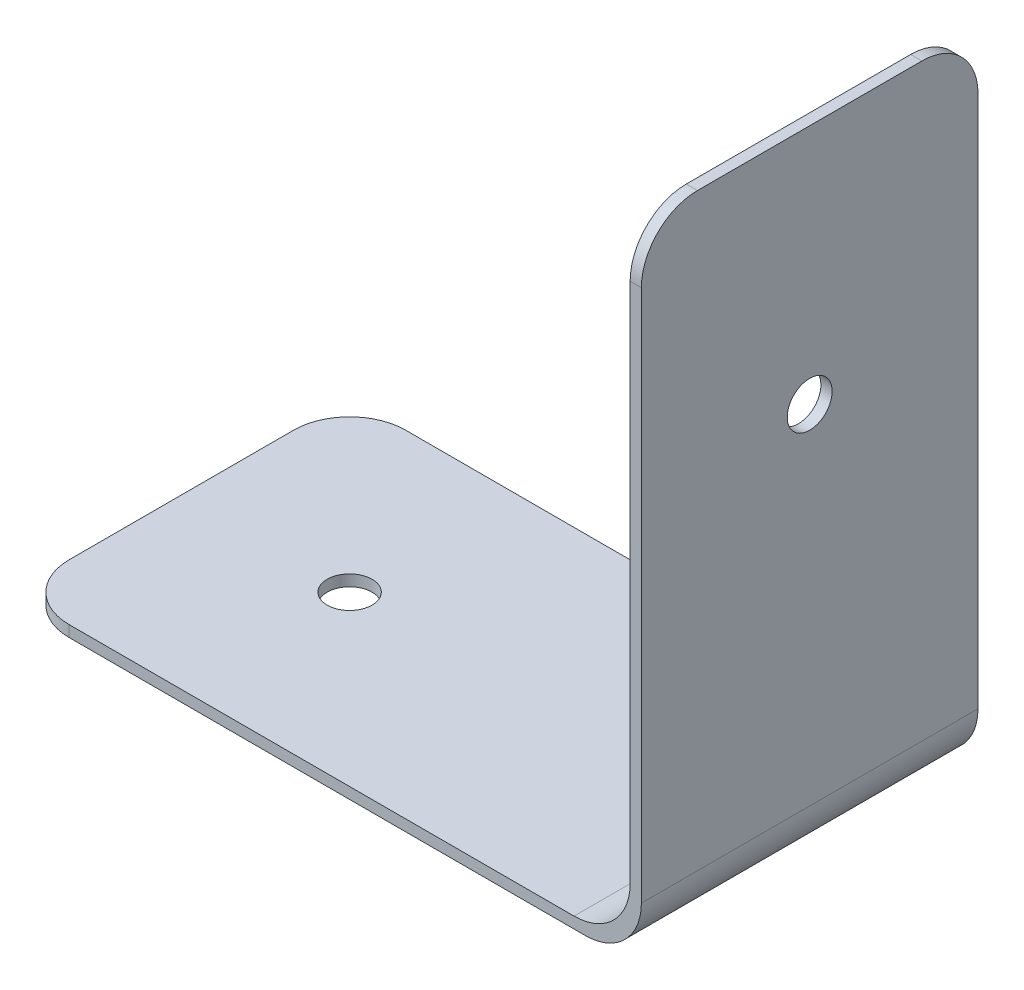
SolidWorks part; units mm, degrees
ref_plane "Front Plane" through (0, 0, 0) normal (0, 0, 1) x (1, 0, 0)
ref_plane "Top Plane" through (0, 0, 0) normal (0, 1, 0) x (1, 0, 0)
ref_plane "Right Plane" through (0, 0, 0) normal (1, 0, 0) x (0, 0, -1)
sketch "Sketch1" plane through (0, 0, 0) normal (0, 0, 1) x (1, 0, 0)
  line L0 (0, 0) -> (102, 0)
  line L1 (112, 10) -> (112, 115)
  line L2 (112, 115) -> (110, 115)
  line L3 (110, 115) -> (110, 12)
  line L4 (0, 0) -> (0, 2)
  line L5 (0, 2) -> (100, 2)
  arc A0 (102, 0) -> (112, 10) centre (102, 10) ccw
  arc A1 (100, 2) -> (110, 12) centre (100, 12) ccw
  dimension "D1" = 10
  dimension "D2" = 2
  dimension "D3" = 2
  dimension "D4" = 100
  dimension "D5" = 105
extrude "Boss-Extrude1" add sketch "Sketch1" along normal blind 60
sketch "Sketch3" plane through (0, 2, 0) normal (0, 1, 0) x (1, 0, 0)
  line L0 (0, -60) -> (0, 0) construction
  circle A0 centre (30, -30) radius 4
  point P4 (0, -30)
  dimension "D1" = 8
  dimension "D2" = 30
extrude "Cut-Extrude1" cut sketch "Sketch3" against normal through all
sketch "Sketch4" plane through (110, 0, 0) normal (-1, 0, 0) x (0, 0, 1)
  line L0 (60, 12) -> (0, 12) construction
  circle A0 centre (30, 72) radius 4
  point P4 (30, 12)
  dimension "D1" = 8
  dimension "D2" = 60
  dimension "D3" = 60
extrude "Cut-Extrude2" cut sketch "Sketch4" against normal through all
fillet "Fillet3" radius 10 2 edges at (111, 115, 0) (111, 115, 60)
fillet "Fillet4" radius 10 2 edges at (0, 1, 0) (0, 1, 60)
